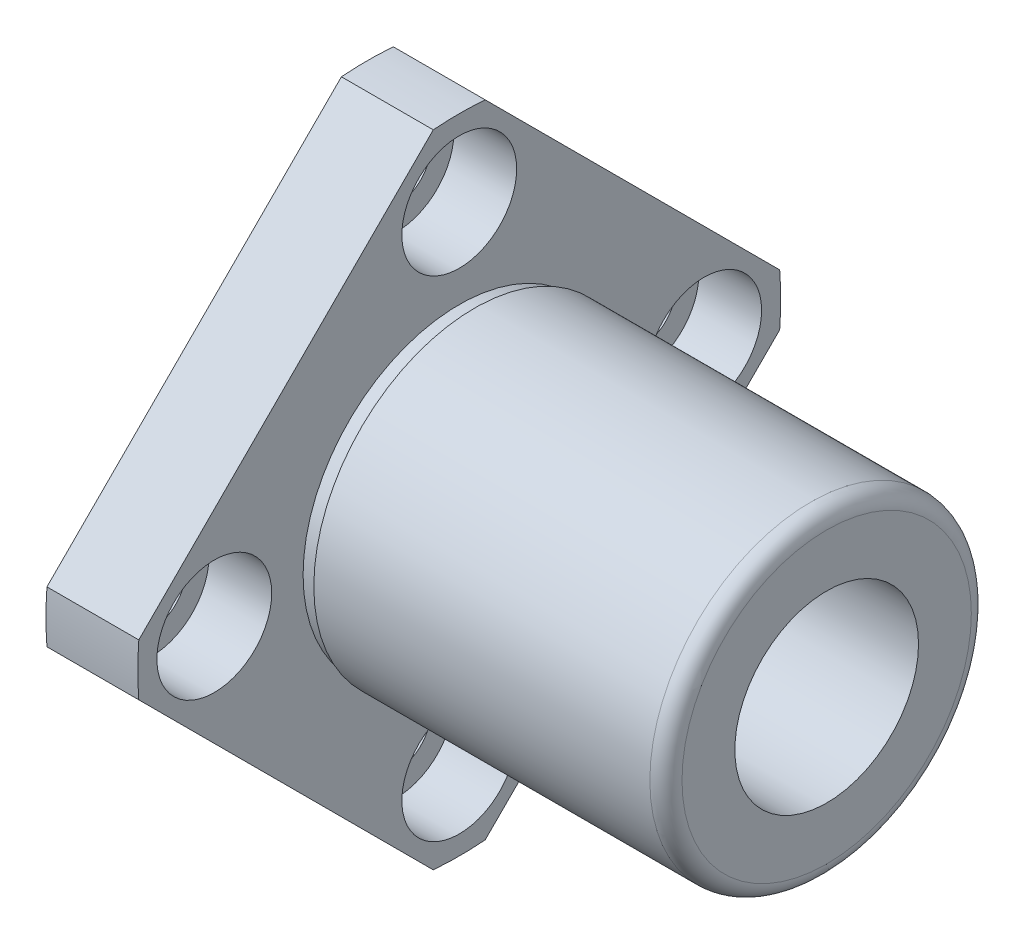
SolidWorks part; units mm, degrees
ref_plane "Front Plane" through (0, 0, 0) normal (0, 0, 1) x (1, 0, 0)
ref_plane "Top Plane" through (0, 0, 0) normal (0, 1, 0) x (1, 0, 0)
ref_plane "Right Plane" through (0, 0, 0) normal (1, 0, 0) x (0, 0, -1)
ref_plane "Plane1" through (0, 0, 0) normal (-1, 0, 0) x (0, -1, 0)
sketch "Sketch1" plane through (0, 0, 0) normal (-1, 0, 0) x (0, -1, 0)
  line L0 (-1.696, 20.9314) -> (-20.9314, 1.696)
  line L1 (-20.9314, -1.696) -> (-1.696, -20.9314)
  line L2 (1.696, -20.9314) -> (20.9314, -1.696)
  line L3 (20.9314, 1.696) -> (1.696, 20.9314)
  arc A0 (1.696, 20.9314) -> (-1.696, 20.9314) centre (0, 0) ccw
  arc A1 (-20.9314, 1.696) -> (-20.9314, -1.696) centre (0, 0) ccw
  arc A2 (-1.696, -20.9314) -> (1.696, -20.9314) centre (0, 0) ccw
  arc A3 (20.9314, -1.696) -> (20.9314, 1.696) centre (0, 0) ccw
extrude "Boss-Extrude1" add sketch "Sketch1" against normal blind 6
ref_plane "Plane2" through (0, 0, 0) normal (0, 0, -1) x (-1, 0, 0)
sketch "Sketch2" plane through (0, 0, 0) normal (0, 0, -1) x (-1, 0, 0)
  line L0 (-30, 9.45) -> (-30, 0)
  line L1 (-30, 0) -> (-6, 0)
  line L2 (-6, 0) -> (-6, 10.2)
  line L3 (-6, 10.2) -> (-7, 10.2)
  line L4 (-7, 10.2) -> (-7, 10.5)
  line L5 (-7, 10.5) -> (-28.95, 10.5)
  line L6 (-30.0013, 0) -> (-6, 0) construction
  arc A0 (-28.95, 10.5) -> (-30, 9.45) centre (-28.95, 9.45) ccw
revolve "Revolve1" add sketch "Sketch2" angle 360 about L6
hole_wizard "CBORE for M4 Hex Head Machine Screw1" positions "Sketch4" profile "Sketch3" counterbore size "M4" standard "ANSI Metric"
sketch "Sketch4" plane through (6, 0, 0) normal (1, 0, 0) x (0, 0, -1)
  point P0 (0, -16)
  point P1 (16, 0)
  point P2 (-16, 0)
  point P3 (0, 16)
sketch "Sketch3" plane through (6, -16, 0) normal (0, 1, 0) x (0, 0, -1)
  line L0 (0, 0) -> (0, 6)
  line L1 (0, 6) -> (2.25, 6)
  line L3 (2.25, 6) -> (2.25, 4.1)
  line L4 (2.25, 4.1) -> (3.75, 4.1)
  line L5 (3.75, 4.1) -> (3.75, 0)
  line L7 (3.75, 0) -> (0, 0)
  line L11 (0, -6.35) -> (0, 107.95) construction
  dimension "Thru Hole Dia." = 4.5
  dimension "Thru Hole Depth" = 6
  dimension "C'Bore Dia." = 7.5
  dimension "C'Bore Depth" = 4.1
hole_wizard "Ø12.0 (12) Diameter Hole1" positions "Sketch6" profile "Sketch5" hole size "Ø12.0" standard "ANSI Metric"
sketch "Sketch6" plane through (30, 0, 0) normal (1, 0, 0) x (0, 0, -1)
  point P0 (0, 0)
sketch "Sketch5" plane through (30, 0, 0) normal (0, 1, 0) x (0, 0, -1)
  line L0 (0, 0) -> (0, 30)
  line L1 (0, 30) -> (6, 30)
  line L2 (6, 30) -> (6, 0)
  line L5 (6, 0) -> (0, 0)
  line L11 (0, -6.35) -> (0, 107.95) construction
  dimension "Thru Hole Dia." = 12
  dimension "Thru Hole Depth" = 30
